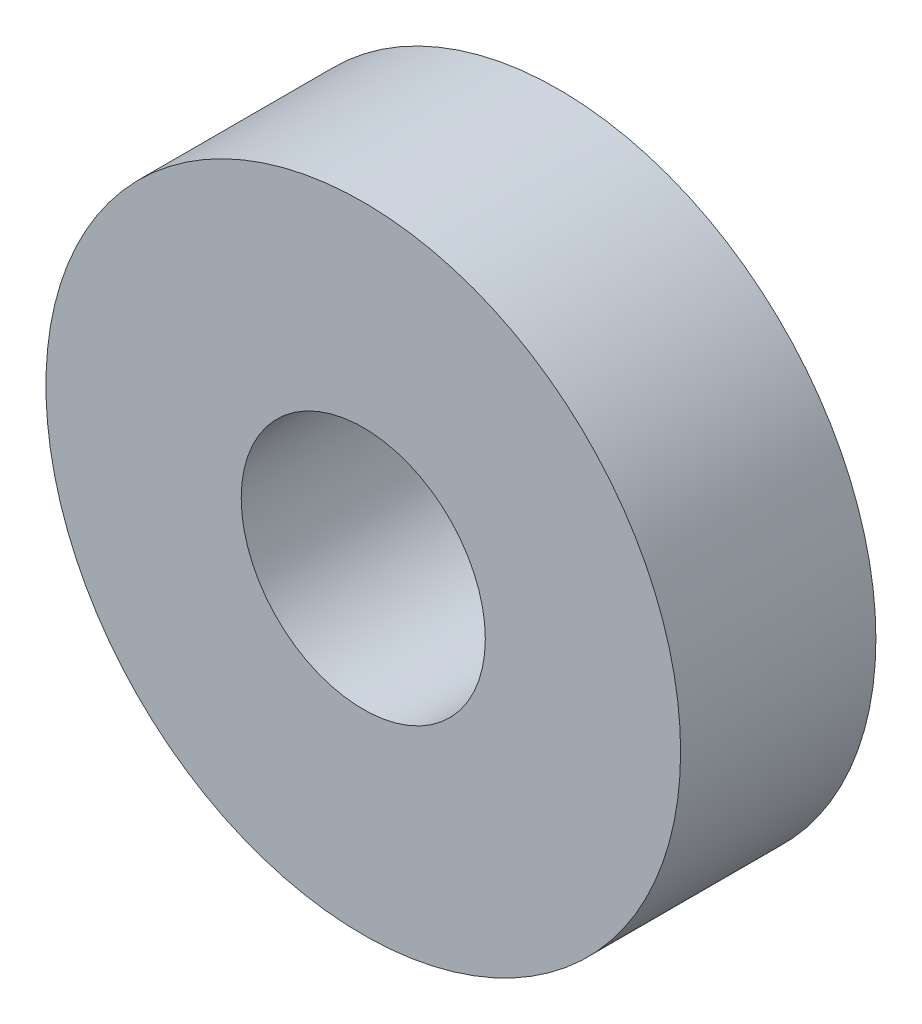
SolidWorks part; units mm, degrees
material "AISI 1018"
ref_plane "Alzado" through (0, 0, 0) normal (0, 0, 1) x (1, 0, 0)
ref_plane "Planta" through (0, 0, 0) normal (0, 1, 0) x (1, 0, 0)
ref_plane "Vista lateral" through (0, 0, 0) normal (1, 0, 0) x (0, 0, -1)
sketch "Croquis1" plane through (0, 0, 0) normal (0, 0, 1) x (1, 0, 0)
  circle A0 centre (0, 0) radius 13
  circle A1 centre (0, 0) radius 5
  dimension "D1" = 26
  dimension "D2" = 10
extrude "Saliente-Extruir1" add sketch "Croquis1" along normal blind 8
